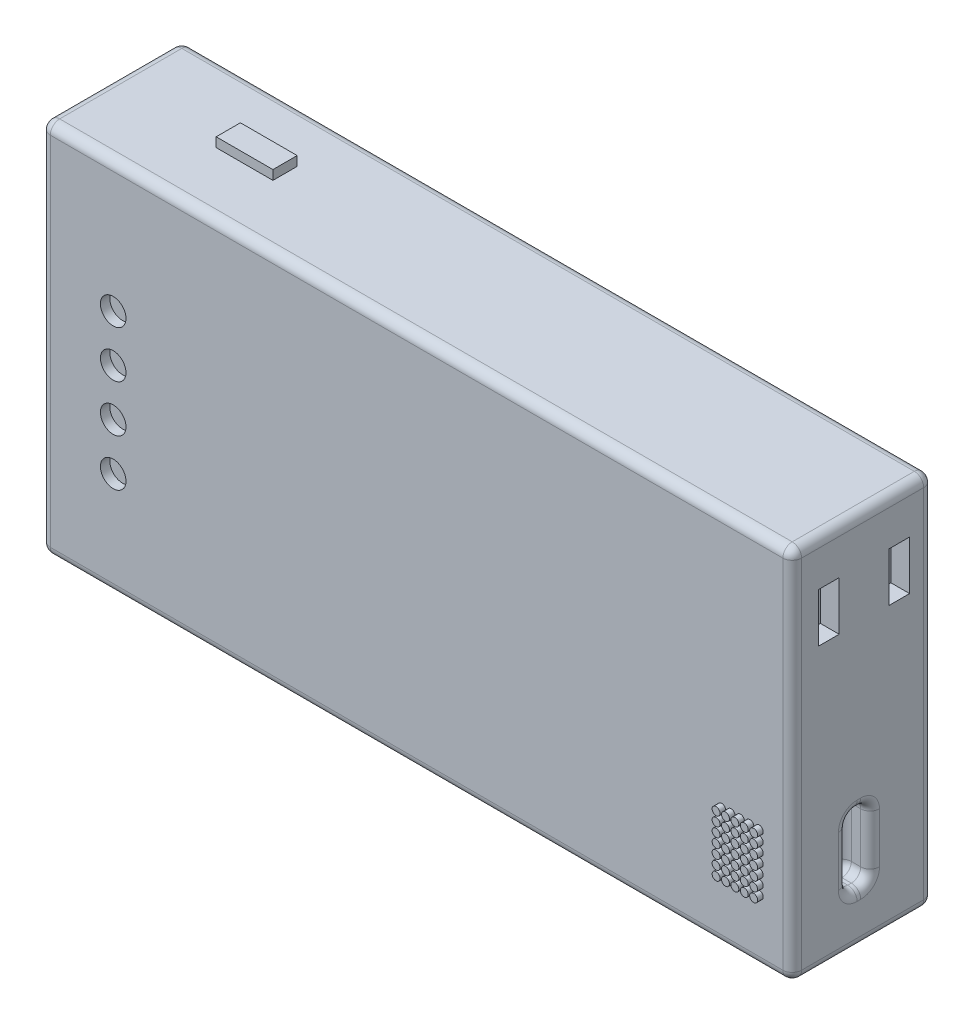
SolidWorks part; units mm, degrees
ref_plane "Front Plane" through (0, 0, 0) normal (0, 0, 1) x (1, 0, 0)
ref_plane "Top Plane" through (0, 0, 0) normal (0, 1, 0) x (1, 0, 0)
ref_plane "Right Plane" through (0, 0, 0) normal (1, 0, 0) x (0, 0, -1)
sketch "Sketch1" plane through (0, 0, 0) normal (0, 0, 1) x (1, 0, 0)
  line L1 (-9.2135, 10.5618) -> (70.7865, 10.5618)
  line L2 (-9.2135, 10.5618) -> (-9.2135, -29.4382)
  line L3 (-9.2135, -29.4382) -> (70.7865, -29.4382)
  line L4 (70.7865, 10.5618) -> (70.7865, -29.4382)
  dimension "D1" = 40
  dimension "D2" = 80
extrude "Boss-Extrude1" add sketch "Sketch1" along normal blind 15
fillet "Fillet2" radius 1 12 edges at (70.7865, -29.4382, 7.5) (30.7865, -29.4382, 0) (70.7865, -9.4382, 0) (70.7865, -9.4382, 15) (30.7865, -29.4382, 15) (-9.2135, -9.4382, 15) (-9.2135, -29.4382, 7.5) (-9.2135, -9.4382, 0) (70.7865, 10.5618, 7.5) (30.7865, 10.5618, 15) (-9.2135, 10.5618, 7.5) (30.7865, 10.5618, 0)
sketch "Sketch2" plane through (0, 10.5618, 0) normal (0, 1, 0) x (1, 0, 0)
  line L1 (2.7671, -5.737) -> (8.8118, -5.737)
  line L2 (2.7671, -5.737) -> (2.7671, -8.3185)
  line L3 (2.7671, -8.3185) -> (8.8118, -8.3185)
  line L4 (8.8118, -5.737) -> (8.8118, -8.3185)
extrude "Boss-Extrude2" add sketch "Sketch2" along normal blind 1
sketch "Sketch3" plane through (0, 0, 15) normal (0, 0, 1) x (1, 0, 0)
  circle A0 centre (-1.5145, -18.32) radius 1.3621
  circle A1 centre (-1.5145, -13.32) radius 1.3621
  circle A2 centre (-1.5145, -8.32) radius 1.3621
  circle A3 centre (-1.5145, -3.32) radius 1.3621
  dimension "D1" = 4
extrude "Cut-Extrude1" cut sketch "Sketch3" against normal blind 1
sketch "Sketch4" plane through (-9.2135, 0, 0) normal (-1, 0, 0) x (0, 0, 1)
  circle A0 centre (6.8318, 4.1746) radius 1.0777
extrude "Cut-Extrude2" cut sketch "Sketch4" against normal blind 1
sketch "Sketch5" plane through (70.7865, 0, 0) normal (1, 0, 0) x (0, 0, -1)
  line L0 (-4.6772, 5.7615) -> (-4.6772, 0.5414)
  line L1 (-12.1772, 5.7615) -> (-10.0056, 5.7615)
  line L2 (-12.1772, 5.7615) -> (-12.1772, 0.5414)
  line L3 (-12.1772, 0.5414) -> (-10.0056, 0.5414)
  line L4 (-10.0056, 5.7615) -> (-10.0056, 0.5414)
  line L5 (-4.6772, 5.7615) -> (-2.5056, 5.7615)
  line L6 (-2.5056, 5.7615) -> (-2.5056, 0.5414)
  line L7 (-4.6772, 0.5414) -> (-2.5056, 0.5414)
  dimension "D1" = 2
extrude "Cut-Extrude3" cut sketch "Sketch5" against normal blind 2
sketch "Sketch6" plane through (70.7865, 0, 0) normal (1, 0, 0) x (0, 0, -1)
  line L1 (-9.0869, -16.7057) -> (-6.7066, -16.7057)
  line L2 (-9.0869, -16.7057) -> (-9.0869, -24.0555)
  line L3 (-9.0869, -24.0555) -> (-6.7066, -24.0555)
  line L4 (-6.7066, -16.7057) -> (-6.7066, -24.0555)
extrude "Cut-Extrude4" cut sketch "Sketch6" against normal blind 3
fillet "Fillet3" radius 1 12 edges at (70.7865, -16.7057, 7.8967) (67.7865, -16.7057, 7.8967) (67.7865, -24.0555, 7.8967) (70.7865, -24.0555, 7.8967) (69.2865, -24.0555, 6.7066) (67.7865, -20.3806, 6.7066) (69.2865, -16.7057, 6.7066) (70.7865, -20.3806, 6.7066) (69.2865, -16.7057, 9.0869) (67.7865, -20.3806, 9.0869) (69.2865, -24.0555, 9.0869) (70.7865, -20.3806, 9.0869)
sketch "Sketch7" plane through (0, 0, 15) normal (0, 0, 1) x (1, 0, 0)
  circle A0 centre (63.2764, -22.7275) radius 0.4224
  circle A1 centre (64.2764, -22.7275) radius 0.4224
  circle A2 centre (65.2764, -22.7275) radius 0.4224
  circle A3 centre (66.2764, -22.7275) radius 0.4224
  circle A4 centre (67.2764, -22.7275) radius 0.4224
  circle A5 centre (64.2764, -21.7275) radius 0.4224
  circle A6 centre (65.2764, -21.7275) radius 0.4224
  circle A7 centre (66.2764, -21.7275) radius 0.4224
  circle A8 centre (67.2764, -21.7275) radius 0.4224
  circle A9 centre (64.2764, -20.7275) radius 0.4224
  circle A10 centre (65.2764, -20.7275) radius 0.4224
  circle A11 centre (66.2764, -20.7275) radius 0.4224
  circle A12 centre (67.2764, -20.7275) radius 0.4224
  circle A13 centre (64.2764, -19.7275) radius 0.4224
  circle A14 centre (65.2764, -19.7275) radius 0.4224
  circle A15 centre (66.2764, -19.7275) radius 0.4224
  circle A16 centre (67.2764, -19.7275) radius 0.4224
  circle A17 centre (64.2764, -18.7275) radius 0.4224
  circle A18 centre (65.2764, -18.7275) radius 0.4224
  circle A19 centre (66.2764, -18.7275) radius 0.4224
  circle A20 centre (67.2764, -18.7275) radius 0.4224
  circle A21 centre (64.2764, -17.7275) radius 0.4224
  circle A22 centre (65.2764, -17.7275) radius 0.4224
  circle A23 centre (66.2764, -17.7275) radius 0.4224
  circle A24 centre (67.2764, -17.7275) radius 0.4224
  circle A25 centre (64.2764, -16.7275) radius 0.4224
  circle A26 centre (65.2764, -16.7275) radius 0.4224
  circle A27 centre (66.2764, -16.7275) radius 0.4224
  circle A28 centre (67.2764, -16.7275) radius 0.4224
  circle A29 centre (63.2764, -21.7275) radius 0.4224
  circle A30 centre (63.2764, -20.7275) radius 0.4224
  circle A31 centre (63.2764, -19.7275) radius 0.4224
  circle A32 centre (63.2764, -18.7275) radius 0.4224
  circle A33 centre (63.2764, -17.7275) radius 0.4224
  circle A34 centre (63.2764, -16.7275) radius 0.4224
  dimension "D1" = 5
  dimension "D2" = 7
extrude "Boss-Extrude3" add sketch "Sketch7" along normal blind 0.6
